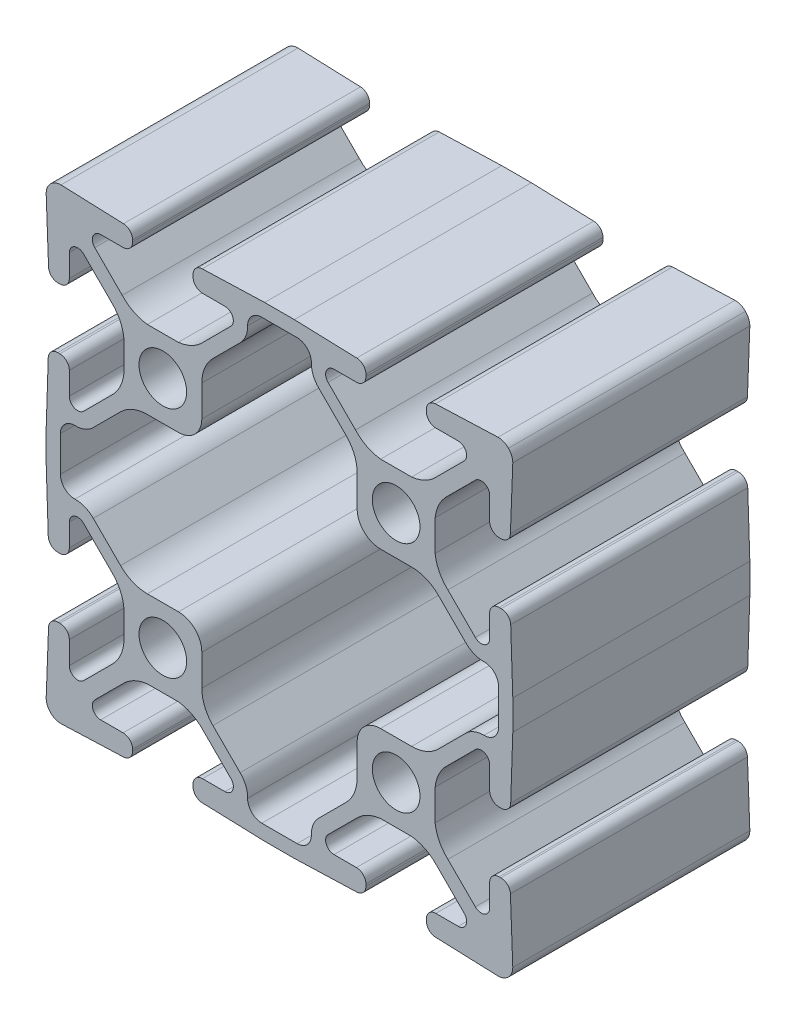
SolidWorks part; units mm, degrees
material "6061 Alloy"
ref_plane "Front" through (0, 0, 0) normal (0, 0, 1) x (1, 0, 0)
ref_plane "Top" through (0, 0, 0) normal (0, 1, 0) x (1, 0, 0)
ref_plane "Right" through (0, 0, 0) normal (1, 0, 0) x (0, 0, -1)
sketch "Sketch1" plane through (0, 0, 0) normal (0, 0, 1) x (1, 0, 0)
  line L0 (14.1585, 16.678) -> (10.8415, 16.678)
  line L1 (8.1446, 18.0451) -> (5.2061, 20.9836)
  line L2 (19.7939, 20.9836) -> (16.8554, 18.0451)
  line L3 (5.8425, 22.52) -> (8.2455, 22.52)
  line L4 (16.7545, 22.52) -> (19.1575, 22.52)
  line L5 (9.2615, 23.536) -> (9.2623, 23.7584)
  line L6 (15.7379, 23.7263) -> (15.7385, 23.536)
  line L7 (8.28, 24.7773) -> (1.5875, 25)
  line L8 (23.4135, 25) -> (16.7152, 24.7451)
  line L9 (1.5875, 25) -> (-1.5875, 25)
  line L10 (-1.5875, 25) -> (-8.28, 24.7773)
  line L11 (24.7451, 16.7152) -> (25, 23.4135)
  line L12 (-9.2623, 23.7584) -> (-9.2615, 23.536)
  line L13 (23.536, 15.7385) -> (23.7263, 15.7379)
  line L14 (-8.2455, 22.52) -> (-5.8425, 22.52)
  line L15 (22.52, 19.1575) -> (22.52, 16.7545)
  line L16 (-5.2061, 20.9836) -> (-8.1446, 18.0451)
  line L17 (18.0451, 16.8554) -> (20.9836, 19.7939)
  line L18 (-10.8415, 16.678) -> (-14.1585, 16.678)
  line L19 (16.678, 10.8415) -> (16.678, 14.1585)
  line L20 (-16.8554, 18.0451) -> (-19.7939, 20.9836)
  line L21 (20.9836, 5.2061) -> (18.0451, 8.1446)
  line L22 (-19.1575, 22.52) -> (-16.7545, 22.52)
  line L23 (22.52, 8.2455) -> (22.52, 5.8425)
  line L24 (-15.7385, 23.536) -> (-15.7379, 23.7263)
  line L25 (23.7584, 9.2623) -> (23.536, 9.2615)
  line L26 (-16.7152, 24.7451) -> (-23.4135, 25)
  line L27 (25, 1.5875) -> (24.7773, 8.28)
  line L28 (25, -1.5875) -> (25, 1.5875)
  line L29 (-25, 23.4135) -> (-24.7451, 16.7152)
  line L30 (24.7773, -8.28) -> (25, -1.5875)
  line L31 (-23.7263, 15.7379) -> (-23.536, 15.7385)
  line L32 (23.536, -9.2615) -> (23.7584, -9.2623)
  line L33 (-22.52, 16.7545) -> (-22.52, 19.1575)
  line L34 (22.52, -5.8425) -> (22.52, -8.2455)
  line L35 (-20.9836, 19.7939) -> (-18.0451, 16.8554)
  line L36 (18.0451, -8.1446) -> (20.9836, -5.2061)
  line L37 (-16.678, 14.1585) -> (-16.678, 10.8415)
  line L38 (16.678, -14.1585) -> (16.678, -10.8415)
  line L39 (-18.0451, 8.1446) -> (-20.9836, 5.2061)
  line L40 (20.9836, -19.7939) -> (18.0451, -16.8554)
  line L41 (-22.52, 5.8425) -> (-22.52, 8.2455)
  line L42 (22.52, -16.7545) -> (22.52, -19.1575)
  line L43 (-23.536, 9.2615) -> (-23.7584, 9.2623)
  line L44 (23.7263, -15.7379) -> (23.536, -15.7385)
  line L45 (-24.7773, 8.28) -> (-25, 1.5875)
  line L46 (25, -23.4135) -> (24.7451, -16.7152)
  line L47 (-25, 1.5875) -> (-25, -1.5875)
  line L48 (-25, -1.5875) -> (-24.7773, -8.28)
  line L49 (16.7152, -24.7451) -> (23.4135, -25)
  line L50 (-23.7584, -9.2623) -> (-23.536, -9.2615)
  line L51 (15.7385, -23.536) -> (15.7379, -23.7263)
  line L52 (-22.52, -8.2455) -> (-22.52, -5.8425)
  line L53 (19.1575, -22.52) -> (16.7545, -22.52)
  line L54 (-20.9836, -5.2061) -> (-18.0451, -8.1446)
  line L55 (16.8554, -18.0451) -> (19.7939, -20.9836)
  line L56 (-16.678, -10.8415) -> (-16.678, -14.1585)
  line L57 (10.8415, -16.678) -> (14.1585, -16.678)
  line L58 (-18.0451, -16.8554) -> (-20.9836, -19.7939)
  line L59 (5.2061, -20.9836) -> (8.1446, -18.0451)
  line L60 (-22.52, -19.1575) -> (-22.52, -16.7545)
  line L61 (8.2455, -22.52) -> (5.8425, -22.52)
  line L62 (-23.536, -15.7385) -> (-23.7263, -15.7379)
  line L63 (9.2623, -23.7584) -> (9.2615, -23.536)
  line L64 (-24.7451, -16.7152) -> (-25, -23.4135)
  line L65 (1.5875, -25) -> (8.28, -24.7773)
  line L66 (-1.5875, -25) -> (1.5875, -25)
  line L67 (-23.4135, -25) -> (-16.7152, -24.7451)
  line L68 (-8.28, -24.7773) -> (-1.5875, -25)
  line L69 (-15.7379, -23.7263) -> (-15.7385, -23.536)
  line L70 (-9.2615, -23.536) -> (-9.2623, -23.7584)
  line L71 (-16.7545, -22.52) -> (-19.1575, -22.52)
  line L72 (-5.8425, -22.52) -> (-8.2455, -22.52)
  line L73 (-19.7939, -20.9836) -> (-16.8554, -18.0451)
  line L74 (-8.1446, -18.0451) -> (-5.2061, -20.9836)
  line L75 (-14.1585, -16.678) -> (-10.8415, -16.678)
  line L76 (10.822, 8.322) -> (14.1585, 8.322)
  line L77 (8.322, 14.1585) -> (8.322, 10.822)
  line L78 (17.0322, 7.1317) -> (19.9494, 4.2144)
  line L79 (4.2144, 19.9494) -> (7.1317, 17.0322)
  line L80 (23.476, 1.8906) -> (23.476, -1.8906)
  line L81 (-1.8906, 23.476) -> (1.8906, 23.476)
  line L82 (19.9494, -4.2144) -> (17.0322, -7.1317)
  line L83 (-7.1317, 17.0322) -> (-4.2144, 19.9494)
  line L84 (14.1585, -8.322) -> (10.822, -8.322)
  line L85 (-8.322, 10.822) -> (-8.322, 14.1585)
  line L86 (8.322, -10.822) -> (8.322, -14.1585)
  line L87 (-14.1585, 8.322) -> (-10.822, 8.322)
  line L88 (7.1317, -17.0322) -> (4.2144, -19.9494)
  line L89 (-19.9494, 4.2144) -> (-17.0322, 7.1317)
  line L90 (1.8906, -23.476) -> (-1.8906, -23.476)
  line L91 (-23.476, -1.8906) -> (-23.476, 1.8906)
  line L92 (-4.2144, -19.9494) -> (-7.1317, -17.0322)
  line L93 (-17.0322, -7.1317) -> (-19.9494, -4.2144)
  line L94 (-8.322, -14.1585) -> (-8.322, -10.822)
  line L95 (-10.822, -8.322) -> (-14.1585, -8.322)
  arc A0 (8.1446, 18.0451) -> (10.8415, 16.678) centre (11.2979, 20.922) ccw
  arc A1 (14.1585, 16.678) -> (16.8554, 18.0451) centre (13.7021, 20.922) ccw
  arc A2 (5.8425, 22.52) -> (5.2061, 20.9836) centre (5.8425, 21.62) ccw
  arc A3 (19.7939, 20.9836) -> (19.1575, 22.52) centre (19.1575, 21.62) ccw
  arc A4 (8.2455, 22.52) -> (9.2615, 23.536) centre (8.2455, 23.536) ccw
  arc A5 (15.7385, 23.536) -> (16.7545, 22.52) centre (16.7545, 23.536) ccw
  arc A6 (9.2623, 23.7584) -> (8.28, 24.7773) centre (8.2463, 23.7618) ccw
  arc A7 (16.7152, 24.7451) -> (15.7379, 23.7263) centre (16.7539, 23.7298) ccw
  arc A8 (24.5355, 24.5355) -> (23.4135, 25) centre (23.4135, 23.4125) ccw
  arc A9 (25, 23.4135) -> (24.5355, 24.5355) centre (23.4125, 23.4135) ccw
  arc A10 (-8.28, 24.7773) -> (-9.2623, 23.7584) centre (-8.2463, 23.7618) ccw
  arc A11 (23.7263, 15.7379) -> (24.7451, 16.7152) centre (23.7298, 16.7539) ccw
  arc A12 (-9.2615, 23.536) -> (-8.2455, 22.52) centre (-8.2455, 23.536) ccw
  arc A13 (22.52, 16.7545) -> (23.536, 15.7385) centre (23.536, 16.7545) ccw
  arc A14 (-5.2061, 20.9836) -> (-5.8425, 22.52) centre (-5.8425, 21.62) ccw
  arc A15 (22.52, 19.1575) -> (20.9836, 19.7939) centre (21.62, 19.1575) ccw
  arc A16 (-10.8415, 16.678) -> (-8.1446, 18.0451) centre (-11.2979, 20.922) ccw
  arc A17 (18.0451, 16.8554) -> (16.678, 14.1585) centre (20.922, 13.7021) ccw
  arc A18 (-16.8554, 18.0451) -> (-14.1585, 16.678) centre (-13.7021, 20.922) ccw
  arc A19 (16.678, 10.8415) -> (18.0451, 8.1446) centre (20.922, 11.2979) ccw
  arc A20 (-19.1575, 22.52) -> (-19.7939, 20.9836) centre (-19.1575, 21.62) ccw
  arc A21 (20.9836, 5.2061) -> (22.52, 5.8425) centre (21.62, 5.8425) ccw
  arc A22 (-16.7545, 22.52) -> (-15.7385, 23.536) centre (-16.7545, 23.536) ccw
  arc A23 (23.536, 9.2615) -> (22.52, 8.2455) centre (23.536, 8.2455) ccw
  arc A24 (-15.7379, 23.7263) -> (-16.7152, 24.7451) centre (-16.7539, 23.7298) ccw
  arc A25 (24.7773, 8.28) -> (23.7584, 9.2623) centre (23.7618, 8.2463) ccw
  arc A26 (-23.4135, 25) -> (-24.5355, 24.5355) centre (-23.4135, 23.4125) ccw
  arc A27 (-24.5355, 24.5355) -> (-25, 23.4135) centre (-23.4125, 23.4135) ccw
  arc A28 (-24.7451, 16.7152) -> (-23.7263, 15.7379) centre (-23.7298, 16.7539) ccw
  arc A29 (23.7584, -9.2623) -> (24.7773, -8.28) centre (23.7618, -8.2463) ccw
  arc A30 (-23.536, 15.7385) -> (-22.52, 16.7545) centre (-23.536, 16.7545) ccw
  arc A31 (22.52, -8.2455) -> (23.536, -9.2615) centre (23.536, -8.2455) ccw
  arc A32 (-20.9836, 19.7939) -> (-22.52, 19.1575) centre (-21.62, 19.1575) ccw
  arc A33 (22.52, -5.8425) -> (20.9836, -5.2061) centre (21.62, -5.8425) ccw
  arc A34 (-16.678, 14.1585) -> (-18.0451, 16.8554) centre (-20.922, 13.7021) ccw
  arc A35 (18.0451, -8.1446) -> (16.678, -10.8415) centre (20.922, -11.2979) ccw
  arc A36 (-18.0451, 8.1446) -> (-16.678, 10.8415) centre (-20.922, 11.2979) ccw
  arc A37 (16.678, -14.1585) -> (18.0451, -16.8554) centre (20.922, -13.7021) ccw
  arc A38 (-22.52, 5.8425) -> (-20.9836, 5.2061) centre (-21.62, 5.8425) ccw
  arc A39 (20.9836, -19.7939) -> (22.52, -19.1575) centre (21.62, -19.1575) ccw
  arc A40 (-22.52, 8.2455) -> (-23.536, 9.2615) centre (-23.536, 8.2455) ccw
  arc A41 (23.536, -15.7385) -> (22.52, -16.7545) centre (23.536, -16.7545) ccw
  arc A42 (-23.7584, 9.2623) -> (-24.7773, 8.28) centre (-23.7618, 8.2463) ccw
  arc A43 (24.7451, -16.7152) -> (23.7263, -15.7379) centre (23.7298, -16.7539) ccw
  arc A44 (24.5355, -24.5355) -> (25, -23.4135) centre (23.4125, -23.4135) ccw
  arc A45 (23.4135, -25) -> (24.5355, -24.5355) centre (23.4135, -23.4125) ccw
  arc A46 (-24.7773, -8.28) -> (-23.7584, -9.2623) centre (-23.7618, -8.2463) ccw
  arc A47 (15.7379, -23.7263) -> (16.7152, -24.7451) centre (16.7539, -23.7298) ccw
  arc A48 (-23.536, -9.2615) -> (-22.52, -8.2455) centre (-23.536, -8.2455) ccw
  arc A49 (16.7545, -22.52) -> (15.7385, -23.536) centre (16.7545, -23.536) ccw
  arc A50 (-20.9836, -5.2061) -> (-22.52, -5.8425) centre (-21.62, -5.8425) ccw
  arc A51 (19.1575, -22.52) -> (19.7939, -20.9836) centre (19.1575, -21.62) ccw
  arc A52 (-16.678, -10.8415) -> (-18.0451, -8.1446) centre (-20.922, -11.2979) ccw
  arc A53 (16.8554, -18.0451) -> (14.1585, -16.678) centre (13.7021, -20.922) ccw
  arc A54 (-18.0451, -16.8554) -> (-16.678, -14.1585) centre (-20.922, -13.7021) ccw
  arc A55 (10.8415, -16.678) -> (8.1446, -18.0451) centre (11.2979, -20.922) ccw
  arc A56 (-22.52, -19.1575) -> (-20.9836, -19.7939) centre (-21.62, -19.1575) ccw
  arc A57 (5.2061, -20.9836) -> (5.8425, -22.52) centre (5.8425, -21.62) ccw
  arc A58 (-22.52, -16.7545) -> (-23.536, -15.7385) centre (-23.536, -16.7545) ccw
  arc A59 (9.2615, -23.536) -> (8.2455, -22.52) centre (8.2455, -23.536) ccw
  arc A60 (-23.7263, -15.7379) -> (-24.7451, -16.7152) centre (-23.7298, -16.7539) ccw
  arc A61 (8.28, -24.7773) -> (9.2623, -23.7584) centre (8.2463, -23.7618) ccw
  arc A62 (-25, -23.4135) -> (-24.5355, -24.5355) centre (-23.4125, -23.4135) ccw
  arc A63 (-24.5355, -24.5355) -> (-23.4135, -25) centre (-23.4135, -23.4125) ccw
  arc A64 (-16.7152, -24.7451) -> (-15.7379, -23.7263) centre (-16.7539, -23.7298) ccw
  arc A65 (-9.2623, -23.7584) -> (-8.28, -24.7773) centre (-8.2463, -23.7618) ccw
  arc A66 (-15.7385, -23.536) -> (-16.7545, -22.52) centre (-16.7545, -23.536) ccw
  arc A67 (-8.2455, -22.52) -> (-9.2615, -23.536) centre (-8.2455, -23.536) ccw
  arc A68 (-19.7939, -20.9836) -> (-19.1575, -22.52) centre (-19.1575, -21.62) ccw
  arc A69 (-5.8425, -22.52) -> (-5.2061, -20.9836) centre (-5.8425, -21.62) ccw
  arc A70 (-14.1585, -16.678) -> (-16.8554, -18.0451) centre (-13.7021, -20.922) ccw
  arc A71 (-8.1446, -18.0451) -> (-10.8415, -16.678) centre (-11.2979, -20.922) ccw
  arc A72 (8.322, 10.822) -> (10.822, 8.322) centre (10.822, 10.822) ccw
  arc A73 (17.0322, 7.1317) -> (14.1585, 8.322) centre (14.1585, 4.258) ccw
  arc A74 (8.322, 14.1585) -> (7.1317, 17.0322) centre (4.258, 14.1585) ccw
  arc A75 (19.9494, 4.2144) -> (21.9184, 3.4142) centre (21.8594, 6.0917) ccw
  arc A76 (23.476, 1.8906) -> (21.9184, 3.4142) centre (21.952, 1.8906) ccw
  arc A77 (3.4142, 21.9184) -> (4.2144, 19.9494) centre (6.0917, 21.8594) ccw
  arc A78 (3.4142, 21.9184) -> (1.8906, 23.476) centre (1.8906, 21.952) ccw
  arc A79 (21.9184, -3.4142) -> (23.476, -1.8906) centre (21.952, -1.8906) ccw
  arc A80 (21.9184, -3.4142) -> (19.9494, -4.2144) centre (21.8594, -6.0917) ccw
  arc A81 (-1.8906, 23.476) -> (-3.4142, 21.9184) centre (-1.8906, 21.952) ccw
  arc A82 (-4.2144, 19.9494) -> (-3.4142, 21.9184) centre (-6.0917, 21.8594) ccw
  arc A83 (14.1585, -8.322) -> (17.0322, -7.1317) centre (14.1585, -4.258) ccw
  arc A84 (-7.1317, 17.0322) -> (-8.322, 14.1585) centre (-4.258, 14.1585) ccw
  arc A85 (10.822, -8.322) -> (8.322, -10.822) centre (10.822, -10.822) ccw
  arc A86 (-10.822, 8.322) -> (-8.322, 10.822) centre (-10.822, 10.822) ccw
  arc A87 (7.1317, -17.0322) -> (8.322, -14.1585) centre (4.258, -14.1585) ccw
  arc A88 (-14.1585, 8.322) -> (-17.0322, 7.1317) centre (-14.1585, 4.258) ccw
  arc A89 (4.2144, -19.9494) -> (3.4142, -21.9184) centre (6.0917, -21.8594) ccw
  arc A90 (1.8906, -23.476) -> (3.4142, -21.9184) centre (1.8906, -21.952) ccw
  arc A91 (-21.9184, 3.4142) -> (-19.9494, 4.2144) centre (-21.8594, 6.0917) ccw
  arc A92 (-21.9184, 3.4142) -> (-23.476, 1.8906) centre (-21.952, 1.8906) ccw
  arc A93 (-3.4142, -21.9184) -> (-1.8906, -23.476) centre (-1.8906, -21.952) ccw
  arc A94 (-3.4142, -21.9184) -> (-4.2144, -19.9494) centre (-6.0917, -21.8594) ccw
  arc A95 (-23.476, -1.8906) -> (-21.9184, -3.4142) centre (-21.952, -1.8906) ccw
  arc A96 (-19.9494, -4.2144) -> (-21.9184, -3.4142) centre (-21.8594, -6.0917) ccw
  arc A97 (-8.322, -14.1585) -> (-7.1317, -17.0322) centre (-4.258, -14.1585) ccw
  arc A98 (-17.0322, -7.1317) -> (-14.1585, -8.322) centre (-14.1585, -4.258) ccw
  arc A99 (-8.322, -10.822) -> (-10.822, -8.322) centre (-10.822, -10.822) ccw
  circle A100 centre (-12.5, -12.5) radius 2.5527
  circle A101 centre (-12.5, 12.5) radius 2.5527
  circle A102 centre (12.5, -12.5) radius 2.5527
  circle A103 centre (12.5, 12.5) radius 2.5527
extrude "Extrude1" add sketch "Sketch1" along normal blind 25.4
